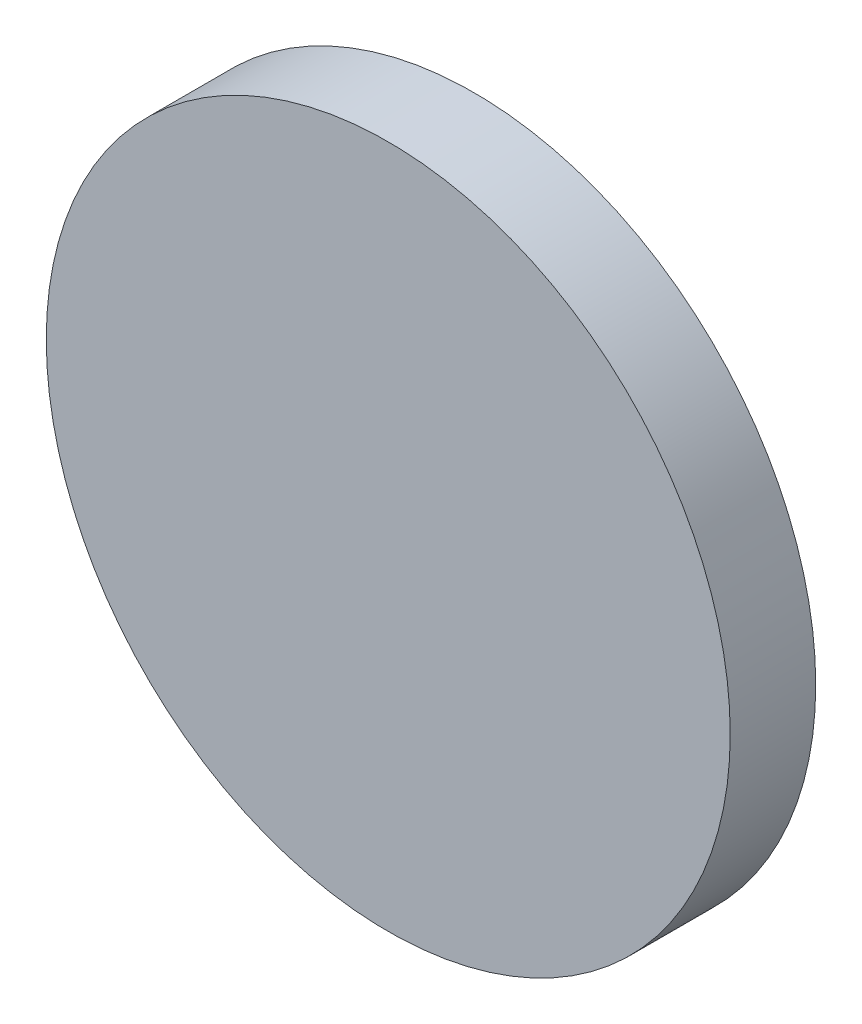
SolidWorks part; units mm, degrees
ref_plane "前视基准面" through (0, 0, 0) normal (0, 0, 1) x (1, 0, 0)
ref_plane "上视基准面" through (0, 0, 0) normal (0, 1, 0) x (1, 0, 0)
ref_plane "右视基准面" through (0, 0, 0) normal (1, 0, 0) x (0, 0, -1)
sketch "草图1" plane through (0, 0, 0) normal (0, 0, 1) x (1, 0, 0)
  circle A0 centre (0, 0) radius 4
  dimension "D1" = 8
extrude "凸台-拉伸1" add sketch "草图1" along normal blind 1 contours A0
